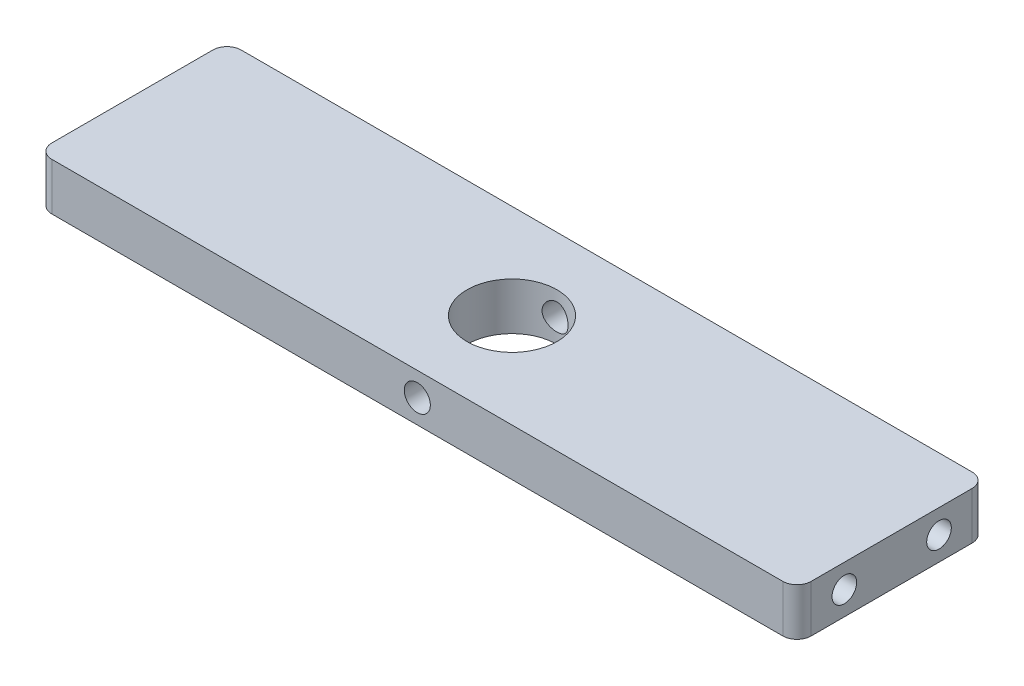
SolidWorks part; units mm, degrees
material "1060 Alloy"
ref_plane "Front Plane" through (0, 0, 0) normal (0, 0, 1) x (1, 0, 0)
ref_plane "Top Plane" through (0, 0, 0) normal (0, 1, 0) x (1, 0, 0)
ref_plane "Right Plane" through (0, 0, 0) normal (1, 0, 0) x (0, 0, -1)
sketch "Sketch1" plane through (0, 0, 0) normal (0, 1, 0) x (1, 0, 0)
  line L1 (80.2, -20) -> (-80.2, -20)
  line L2 (80.2, -20) -> (80.2, 20)
  line L3 (80.2, 20) -> (-80.2, 20)
  line L4 (-80.2, -20) -> (-80.2, 20)
  line L5 (80.2, -20) -> (-80.2, 20) construction
  line L6 (80.2, 20) -> (-80.2, -20) construction
  circle A0 centre (0, 0) radius 9.5
  point P0 (0, 0)
  dimension "D3" = 19
  dimension "D1" = 160.4
  dimension "D2" = 40
extrude "Boss-Extrude1" add sketch "Sketch1" along normal mid plane 10
sketch "Sketch2" plane through (-80.2, 0, 0) normal (-1, 0, 0) x (0, 0, 1)
  line L0 (-20, 0) -> (-10, 0) construction
  line L1 (-20, 5) -> (-20, -5) construction
  line L2 (20, 0) -> (10, 0) construction
  line L3 (20, 5) -> (20, -5) construction
  dimension "D1" = 10
hole_wizard "Tap Drill for M5 Helicoil1" positions "Sketch3" profile "Sketch4" hole size "M5x0.8" standard "ANSI Metric"
sketch "Sketch3" plane through (-80.2, 0, 0) normal (-1, 0, 0) x (0, 0, 1)
  point P0 (-10, 0)
  point P3 (10, 0)
sketch "Sketch4" plane through (-80.2, 0, -10) normal (0, 1, 0) x (0, 0, 1)
  line L0 (0, 0) -> (0, 31.5622)
  line L1 (0, 31.5622) -> (2.6, 30)
  line L2 (2.6, 30) -> (2.6, 0)
  line L5 (2.6, 0) -> (0, 0)
  line L10 (0, 31.5622) -> (-2.6, 30) construction
  line L11 (0, -6.35) -> (0, 107.95) construction
  dimension "Hole Dia." = 5.2
  dimension "Hole Depth" = 30
  dimension "Drill Angle" = 118
mirror "Mirror1" about plane through (0, 0, 0) normal (1, 0, 0) of "Tap Drill for M5 Helicoil1"
fillet "Fillet1" radius 3 4 edges at (80.2, 0, 20) (80.2, 0, -20) (-80.2, 0, 20) (-80.2, 0, -20)
hole_wizard "M5 Clearance Hole1" positions "Sketch6" profile "Sketch7" hole size "M5" standard "ANSI Metric" end condition through all
sketch "Sketch6" plane through (0, 0, -20) normal (0, 0, -1) x (-1, 0, 0)
  point P0 (0, 0)
sketch "Sketch7" plane through (0, 0, -20) normal (1, 0, 0) x (0, 1, 0)
  line L0 (0, 0) -> (0, 40)
  line L1 (0, 40) -> (2.75, 40)
  line L2 (2.75, 40) -> (2.75, 0)
  line L5 (2.75, 0) -> (0, 0)
  line L11 (0, -6.35) -> (0, 107.95) construction
  dimension "Thru Hole Dia." = 5.5
  dimension "Thru Hole Depth" = 40
equation "\"tubeOutDiameter\" = 35mm"
equation "\"wheelShaftDiameter\"= 12mm"
equation "\"wheelThickness\"= 135mm"
equation "\"BearingDiameter\"= 20mm"
equation "\"BearingThickness\"= 10mm"
equation "\"frontShaftDiameter\"= 20mm"
equation "\"D1@Sketch1\"=\"wheelThickness\"+1in"
